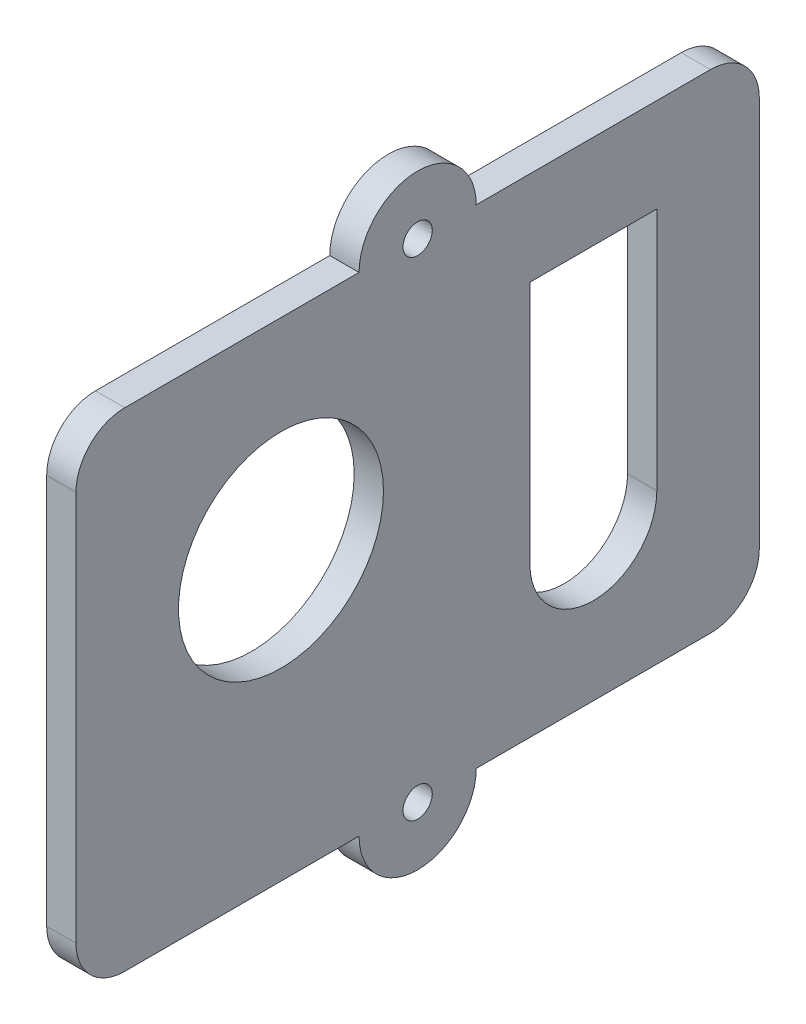
SolidWorks part; units mm, degrees
ref_plane "Front Plane" through (0, 0, 0) normal (0, 0, 1) x (1, 0, 0)
ref_plane "Top Plane" through (0, 0, 0) normal (0, 1, 0) x (1, 0, 0)
ref_plane "Right Plane" through (0, 0, 0) normal (1, 0, 0) x (0, 0, -1)
sketch "Sketch1" plane through (0, 0, 0) normal (1, 0, 0) x (0, 0, -1)
  line L6 (35, -5.3823) -> (35, 34.6177)
  line L7 (-35, 34.6177) -> (-35, -5.3823)
  line L8 (-30, -10.3823) -> (-6, -10.3823)
  line L9 (6, -10.3823) -> (30, -10.3823)
  line L10 (30, 39.6177) -> (6, 39.6177)
  line L11 (-6, 39.6177) -> (-30, 39.6177)
  line L12 (28, 39.6177) -> (-28, 39.6177) construction
  line L13 (35, -5.3823) -> (35, 44.6177) construction
  line L14 (-35, 44.6177) -> (-35, -5.3823) construction
  arc A0 (6, 39.6177) -> (-6, 39.6177) centre (0, 39.6177) ccw construction
  arc A1 (-6, -10.3823) -> (6, -10.3823) centre (0, -10.3823) ccw construction
  arc A2 (-35, -5.3823) -> (-30, -10.3823) centre (-30, -5.3823) ccw construction
  arc A3 (30, -10.3823) -> (35, -5.3823) centre (30, -5.3823) ccw construction
  arc A4 (6, 39.6177) -> (-6, 39.6177) centre (0, 39.6177) ccw
  arc A5 (-6, -10.3823) -> (6, -10.3823) centre (0, -10.3823) ccw
  arc A6 (-35, -5.3823) -> (-30, -10.3823) centre (-30, -5.3823) ccw
  arc A7 (30, -10.3823) -> (35, -5.3823) centre (30, -5.3823) ccw
  arc A8 (30, 39.6177) -> (35, 34.6177) centre (30, 34.6177) cw
  arc A9 (-35, 34.6177) -> (-30, 39.6177) centre (-30, 34.6177) cw
  dimension "D1" = 5
extrude "Boss-Extrude1" add sketch "Sketch1" along normal blind 3
sketch "Sketch2" plane through (3, 0, 0) normal (1, 0, 0) x (0, 0, -1)
  line L1 (11.5, 30) -> (24.5, 30)
  line L2 (11.5, 30) -> (11.5, 5)
  line L4 (24.5, 30) -> (24.5, 5)
  circle A0 centre (0, 39.6177) radius 1.5
  circle A1 centre (0, -10.3823) radius 1.5
  circle A2 centre (-14, 19) radius 10.5
  arc A3 (24.5, 5) -> (11.5, 5) centre (18, 5) cw
  dimension "D1" = 3
  dimension "D2" = 3
  dimension "D3" = 21
  dimension "D4" = 19
  dimension "D5" = 14
  dimension "D6" = 13
  dimension "D7" = 18
  dimension "D8" = 30
  dimension "D9" = 5
extrude "Cut-Extrude1" cut sketch "Sketch2" against normal through all
